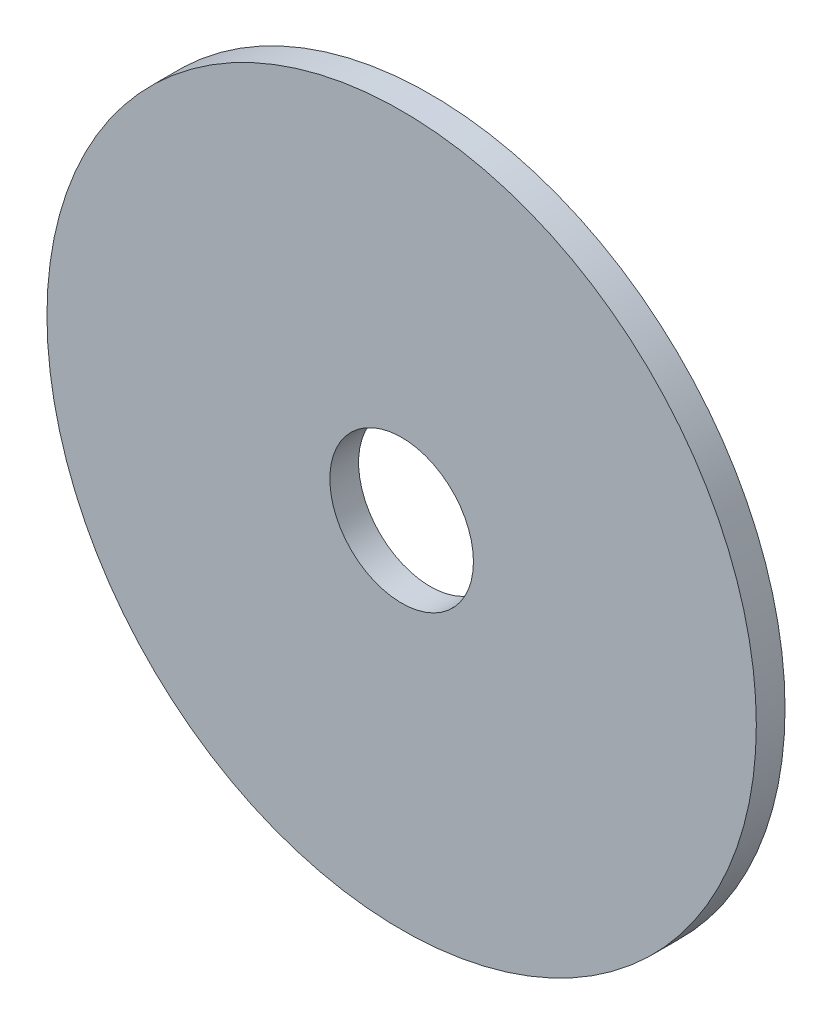
SolidWorks part; units mm, degrees
material "1060 Alloy"
ref_plane "Front Plane" through (0, 0, 0) normal (0, 0, 1) x (1, 0, 0)
ref_plane "Top Plane" through (0, 0, 0) normal (0, 1, 0) x (1, 0, 0)
ref_plane "Right Plane" through (0, 0, 0) normal (1, 0, 0) x (0, 0, -1)
sketch "Sketch1" plane through (0, 0, 0) normal (0, 0, 1) x (1, 0, 0)
  circle A0 centre (0, 0) radius 12.35
  circle A1 centre (0, 0) radius 2.5
  dimension "D1" = 24.7
  dimension "D2" = 5
extrude "Boss-Extrude1" add sketch "Sketch1" along normal blind 1
equation "\"tubeOutDiameter\" = 35mm"
equation "\"wheelShaftDiameter\"= 12mm"
equation "\"wheelThickness\"= 135mm"
equation "\"BearingDiameter\"= 20mm"
equation "\"BearingThickness\"= 10mm"
equation "\"D1@Sketch1\"=\"wheelShaftDiameter\"+0.5in"
